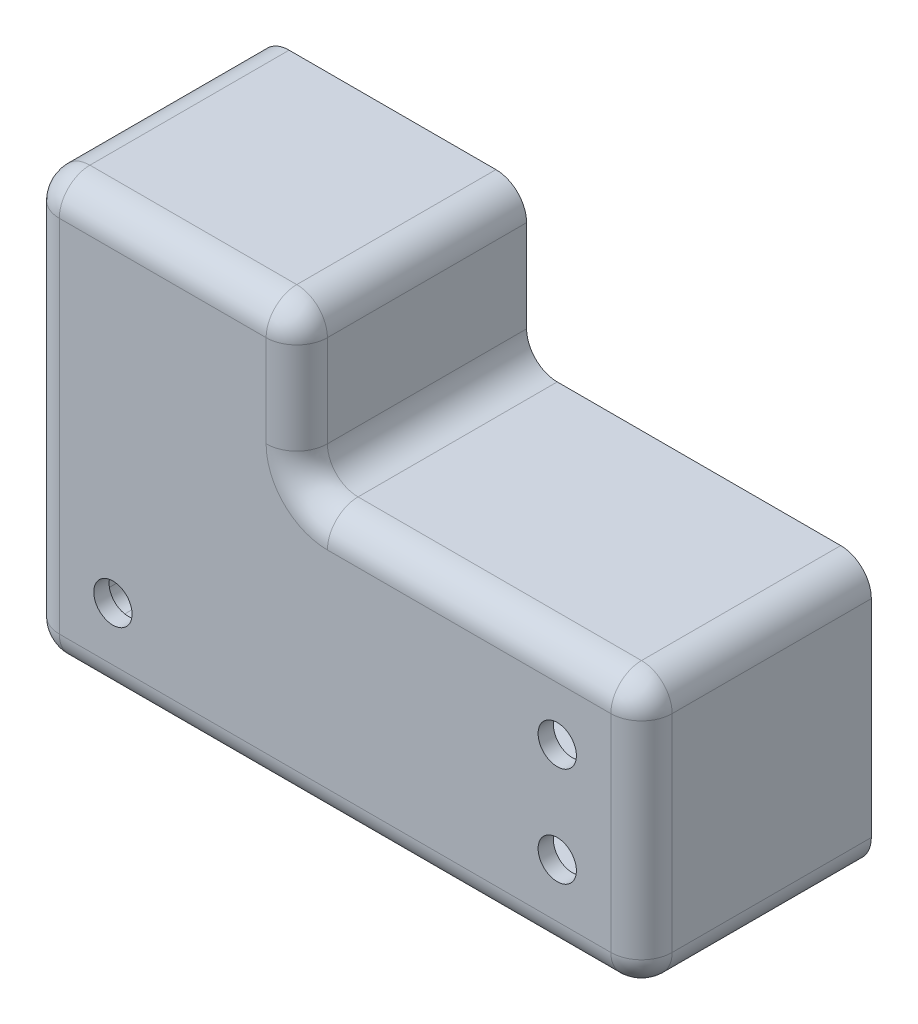
SolidWorks part; units mm, degrees
ref_plane "Front Plane" through (0, 0, 0) normal (0, 0, 1) x (1, 0, 0)
ref_plane "Top Plane" through (0, 0, 0) normal (0, 1, 0) x (1, 0, 0)
ref_plane "Right Plane" through (0, 0, 0) normal (1, 0, 0) x (0, 0, -1)
sketch "Sketch1" plane through (0, 0, 0) normal (0, 0, 1) x (1, 0, 0)
  line L0 (0, 0) -> (0, 69.85)
  line L1 (0, 69.85) -> (44.45, 69.85)
  line L2 (44.45, 69.85) -> (44.45, 44.45)
  line L3 (44.45, 44.45) -> (101.6, 44.45)
  line L4 (101.6, 44.45) -> (101.6, 0)
  line L5 (101.6, 0) -> (0, 0)
  dimension "D1" = 69.85
  dimension "D2" = 101.6
  dimension "D3" = 44.45
  dimension "D4" = 57.15
extrude "Boss-Extrude1" add sketch "Sketch1" along normal blind 38.1
fillet "Fillet1" radius 5.08 6 edges at (101.6, 0, 19.05) (101.6, 44.45, 19.05) (0, 0, 19.05) (0, 69.85, 19.05) (44.45, 69.85, 19.05) (44.45, 44.45, 19.05)
fillet "Fillet2" radius 5.08 12 edges at (100.1121, 42.9621, 38.1) (101.6, 22.225, 38.1) (100.1121, 1.4879, 38.1) (50.8, 0, 38.1) (1.4879, 1.4879, 38.1) (0, 34.925, 38.1) (1.4879, 68.3621, 38.1) (22.225, 69.85, 38.1) (42.9621, 68.3621, 38.1) (44.45, 57.15, 38.1) (45.9379, 45.9379, 38.1) (73.025, 44.45, 38.1)
shell "Shell1" thickness 2.54
hole_wizard "#97 (0.0059) Diameter Hole1" positions "Sketch3" profile "Sketch2" hole size "#97" standard "ANSI Inch" end condition through all
sketch "Sketch3" plane through (0, 0, 38.1) normal (0, 0, 1) x (1, 0, 0)
  line L0 (96.52, 39.37) -> (49.53, 39.37) construction
  line L1 (96.52, 5.08) -> (96.52, 39.37) construction
  point P0 (87.63, 30.48)
  dimension "D1" = 8.89
  dimension "D2" = 8.89
sketch "Sketch2" plane through (87.63, 30.48, 38.1) normal (1, 0, 0) x (0, -1, 0)
  line L0 (0, 0) -> (0, 38.1)
  line L1 (0, 38.1) -> (3.175, 38.1)
  line L2 (3.175, 38.1) -> (3.175, 0)
  line L5 (3.175, 0) -> (0, 0)
  line L11 (0, -6.35) -> (0, 107.95) construction
  dimension "Thru Hole Dia." = 6.35
  dimension "Thru Hole Depth" = 38.1
hole_wizard "1/4 (0.25) Diameter Hole1" positions "Sketch5" profile "Sketch4" hole size "1/4" standard "ANSI Inch" end condition through all
sketch "Sketch5" plane through (0, 0, 38.1) normal (0, 0, 1) x (1, 0, 0)
  line L0 (5.08, 5.08) -> (96.52, 5.08) construction
  line L1 (5.08, 64.77) -> (5.08, 5.08) construction
  circle A0 centre (87.63, 30.48) radius 3.175 construction
  point P0 (87.63, 13.97)
  point P2 (13.97, 13.97)
  dimension "D1" = 8.89
  dimension "D2" = 8.89
  dimension "D3" = 8.89
  dimension "D4" = 0
sketch "Sketch4" plane through (87.63, 13.97, 38.1) normal (1, 0, 0) x (0, -1, 0)
  line L0 (0, 0) -> (0, 38.1)
  line L1 (0, 38.1) -> (3.175, 38.1)
  line L2 (3.175, 38.1) -> (3.175, 0)
  line L5 (3.175, 0) -> (0, 0)
  line L11 (0, -6.35) -> (0, 107.95) construction
  dimension "Thru Hole Dia." = 6.35
  dimension "Thru Hole Depth" = 38.1
